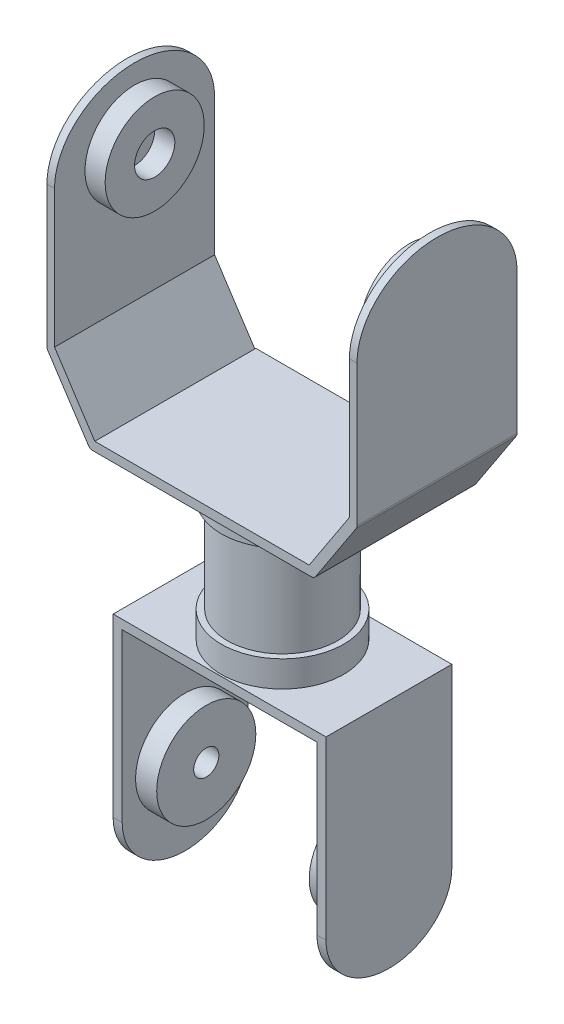
SolidWorks part; units mm, degrees
ref_plane "Front Plane" through (0, 0, 0) normal (0, 0, 1) x (1, 0, 0)
ref_plane "Top Plane" through (0, 0, 0) normal (0, 1, 0) x (1, 0, 0)
ref_plane "Right Plane" through (0, 0, 0) normal (1, 0, 0) x (0, 0, -1)
sketch "Sketch2" plane through (0, 0, 0) normal (0, 1, 0) x (1, 0, 0)
  line L1 (-21.3, 16) -> (21.3, 16)
  line L2 (-21.3, 16) -> (-21.3, -16)
  line L3 (-21.3, -16) -> (21.3, -16)
  line L4 (21.3, 16) -> (21.3, -16)
  line L5 (-21.3, 16) -> (21.3, -16) construction
  line L6 (-21.3, -16) -> (21.3, 16) construction
  point P0 (0, 0)
  dimension "D1" = 32
  dimension "D2" = 42.6
extrude "Boss-Extrude1" add sketch "Sketch2" along normal blind 1.8
sketch "Sketch3" plane through (0, 0, 16) normal (0, 0, 1) x (1, 0, 0)
  line L0 (0, 0) -> (0, 14) construction
  line L1 (0, 14) -> (21.3, 14) construction
  line L2 (21.3, 14) -> (21.3, 0) construction
  line L3 (21.3, 14) -> (29.3, 14) construction
  line L4 (21.3, 1.8) -> (29.3, 14)
  line L6 (30.8052, 13.013) -> (22.2722, 0)
  line L7 (22.2722, 0) -> (21.3, 0)
  line L8 (21.3, 0) -> (21.3, 1.8)
  line L10 (30.8052, 14) -> (29.3, 14)
  line L11 (30.8052, 14) -> (30.8052, 13.013)
  dimension "D1" = 14
  dimension "D2" = 8
  dimension "D3" = 1.8
  dimension "D4" = 0.987
  dimension "D5" = 15.5612
extrude "Boss-Extrude2" add sketch "Sketch3" against normal blind 31.8
fillet "Fillet1" radius 1 2 edges at (30.8052, 13.013, 0.1) (22.2722, 0, 0.1)
sketch "Sketch4" plane through (0, 14, 0) normal (0, 1, 0) x (1, 0, 0)
  line L0 (30.8052, 15.8) -> (30.8052, -16) construction
  line L1 (29.3, 15.8) -> (30.8052, 15.8)
  line L2 (29.3, 15.8) -> (29.3, -16)
  line L3 (29.3, -16) -> (30.8052, -16)
  line L4 (30.8052, 15.8) -> (30.8052, -16)
extrude "Boss-Extrude3" add sketch "Sketch4" along normal blind 41
sketch "Sketch5" plane through (30.8052, 0, 0) normal (1, 0, 0) x (0, 0, -1)
  line L0 (-0.1, 13.3116) -> (-0.1, 41.3116) construction
  line L1 (-16, 13.3116) -> (15.8, 13.3116) construction
  line L2 (15.8, 13.3116) -> (15.8, 55) construction
  line L3 (-16, 41.3116) -> (15.8, 41.3116) construction
  line L4 (-0.1, 55) -> (-0.1, 41.3116) construction
  line L5 (-16, 41.3116) -> (-16, 55)
  line L6 (-16, 55) -> (15.8, 55) construction
  line L7 (-16, 13.3116) -> (-16, 55) construction
  line L8 (-16, 55) -> (-0.1, 55)
  line L9 (-0.1, 55) -> (15.8, 55)
  line L10 (15.8, 55) -> (15.8, 41.3116)
  ellipse E0 centre (-0.1, 41.3116) end of major axis (15.8, 41.3116) minor radius 13.6884 (15.8, 41.3116) -> (-16, 41.3116) ccw
  line M2 (-16, 55) -> (-16, 13.3116)
  line M4 (15.8, 13.3116) -> (15.8, 55)
  line M5 (15.8, 55) -> (-16, 55)
  dimension "D1" = 28
extrude "Cut-Extrude1" cut sketch "Sketch5" against normal blind 41 contours E0 M5 M2 | E0 M4 M5
sketch "Sketch7" plane through (29.3, 0, 0) normal (-1, 0, 0) x (0, 0, 1)
  line L0 (0.1, 55) -> (0.1, 41.3116) construction
  circle A0 centre (0.1, 41.3116) radius 9.85
  circle A1 centre (0.1, 41.3116) radius 4
  ellipse E0 centre (0.1, 41.3116) end of major axis (-15.8, 41.3116) minor radius 13.6884 (16, 41.3116) -> (-15.8, 41.3116) ccw construction
  dimension "D1" = 19.7
  dimension "D2" = 8
extrude "Boss-Extrude4" add sketch "Sketch7" along normal blind 4
mirror "Mirror2" about plane through (0, 0, 0) normal (1, 0, 0) of "Boss-Extrude2", "Fillet1", "Boss-Extrude3", "Cut-Extrude1", "Boss-Extrude4"
sketch "Sketch8" plane through (0, 0, 0) normal (0, -1, 0) x (1, 0, 0)
  circle A0 centre (0, 0) radius 12.15
  dimension "D1" = 24.3
extrude "Boss-Extrude5" add sketch "Sketch8" along normal blind 5.4
sketch "Sketch9" plane through (0, -5.4, 0) normal (0, -1, 0) x (1, 0, 0)
  circle A0 centre (0, 0) radius 10.95
  dimension "D1" = 21.9
extrude "Boss-Extrude6" add sketch "Sketch9" along normal blind 19
sketch "Sketch11" plane through (0, -24.4, 0) normal (0, -1, 0) x (1, 0, 0)
  circle A0 centre (0, 0) radius 12.15
extrude "Boss-Extrude7" add sketch "Sketch11" along normal blind 5.2
sketch "Sketch12" plane through (0, -29.6, 0) normal (0, -1, 0) x (1, 0, 0)
  line L1 (-21.15, 12.5) -> (21.15, 12.5)
  line L2 (-21.15, 12.5) -> (-21.15, -12.5)
  line L3 (-21.15, -12.5) -> (21.15, -12.5)
  line L4 (21.15, 12.5) -> (21.15, -12.5)
  line L5 (-21.15, 12.5) -> (21.15, -12.5) construction
  line L6 (-21.15, -12.5) -> (21.15, 12.5) construction
  point P0 (0, 0)
  dimension "D1" = 25
  dimension "D2" = 42.3
extrude "Boss-Extrude8" add sketch "Sketch12" along normal blind 1.8
sketch "Sketch13" plane through (0, -31.4, 0) normal (0, -1, 0) x (1, 0, 0)
  line L6 (-21.15, 12.5) -> (-19.35, 12.5)
  line L7 (-21.15, 12.5) -> (-21.15, -12.5)
  line L8 (-21.15, -12.5) -> (-19.35, -12.5)
  line L9 (-19.35, 12.5) -> (-19.35, -12.5)
  line L10 (-21.15, -12.5) -> (21.15, -12.5) construction
  dimension "D1" = 25
  dimension "D2" = 1.8
extrude "Boss-Extrude9" add sketch "Sketch13" along normal blind 44.3
sketch "Sketch16" plane through (-21.15, 0, 0) normal (-1, 0, 0) x (0, 0, 1)
  line L0 (0, -75.7) -> (0, -64.6) construction
  line L1 (12.5, -75.7) -> (-12.5, -75.7) construction
  line L2 (12.5, -75.7) -> (12.5, -29.6) construction
  line L3 (-12.5, -64.6) -> (-12.5, -75.7)
  line L4 (-12.5, -75.7) -> (12.5, -75.7)
  line L5 (12.5, -75.7) -> (12.5, -64.6)
  line L6 (-12.5, -64.6) -> (12.5, -64.6)
  ellipse E0 centre (0, -64.6) end of major axis (12.5, -64.6) minor radius 11.1 (-12.5, -64.6) -> (12.5, -64.6) ccw
  line M2 (-12.5, -29.6) -> (-12.5, -75.7)
  line M3 (-12.5, -75.7) -> (12.5, -75.7)
  line M4 (12.5, -75.7) -> (12.5, -29.6)
  dimension "D1" = 11.1
extrude "Cut-Extrude5" cut sketch "Sketch16" against normal blind 44.3 contours E0 M2 M3 | E0 L4 M4
sketch "Sketch18" plane through (-19.35, 0, 0) normal (1, 0, 0) x (0, 0, -1)
  line L0 (0, -75.7) -> (0, -58.4) construction
  circle A0 centre (0, -58.4) radius 9.85
  circle A1 centre (0, -58.4) radius 2.5
  ellipse E0 centre (0, -64.6) end of major axis (-12.5, -64.6) minor radius 11.1 (-12.5, -64.6) -> (12.5, -64.6) ccw construction
  dimension "D2" = 19.7
  dimension "D3" = 5
  dimension "D1" = 17.3
extrude "Boss-Extrude10" add sketch "Sketch18" along normal blind 4.2
mirror "Mirror3" about plane through (0, 0, 0) normal (1, 0, 0) of "Boss-Extrude9", "Cut-Extrude5", "Boss-Extrude10"
